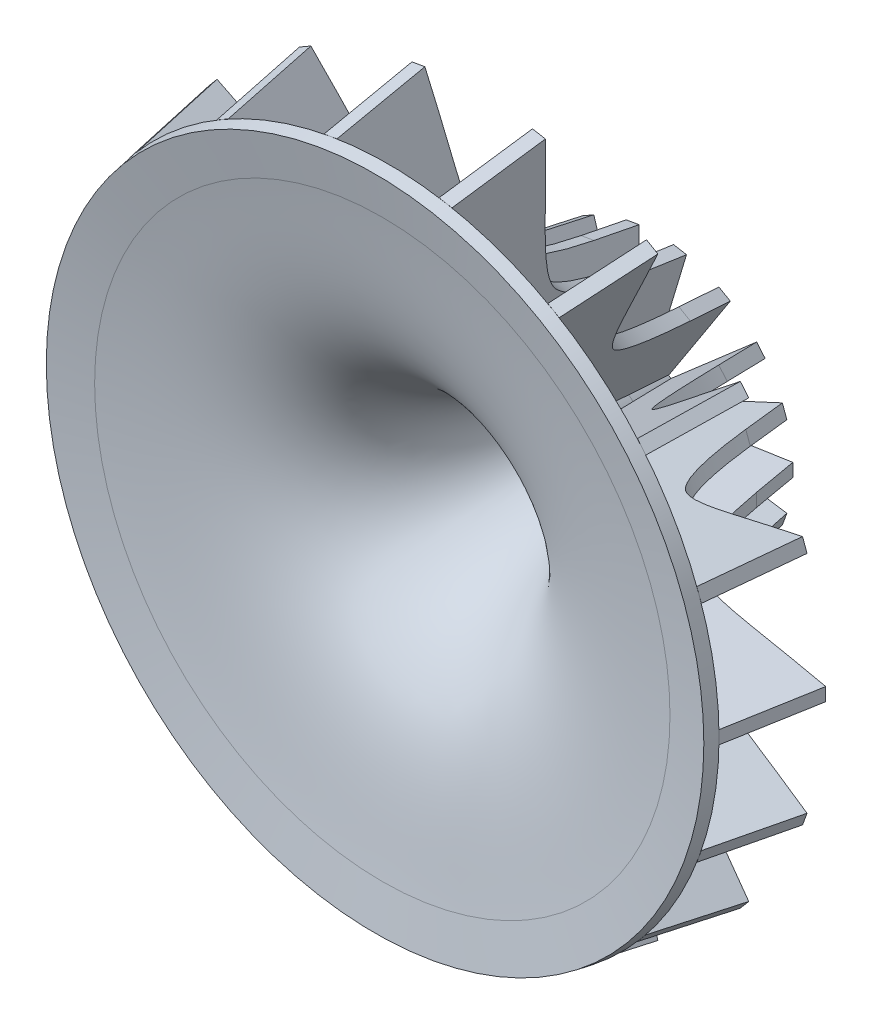
SolidWorks part; units mm, degrees
ref_plane "Front Plane" through (0, 0, 0) normal (0, 0, 1) x (1, 0, 0)
ref_plane "Top Plane" through (0, 0, 0) normal (0, 1, 0) x (1, 0, 0)
ref_plane "Right Plane" through (0, 0, 0) normal (1, 0, 0) x (0, 0, -1)
sketch "Sketch_of_Hub" plane through (0, 0, 0) normal (0, 1, 0) x (1, 0, 0)
  line L0 (-25, 0) -> (-21.875, 0.551)
  line L1 (-25, 0) -> (-2.5, 0) construction
  line L2 (-3.0878, 16.6667) -> (-2.5, 20)
  line L3 (-2.5, 0) -> (-2.5, 20) construction
  line L4 (-25.1736, 0.9848) -> (-22.0486, 1.5358)
  line L5 (-4.0726, 16.8403) -> (-3.4848, 20.1736)
  line L6 (-3.4848, 20.1736) -> (-2.5, 20)
  line L7 (-25.1736, 0.9848) -> (-25, 0)
  line L8 (0, -11.4107) -> (0, -1.4179) construction
  spline S0 degree 1 poles (-22.0486, 1.5358) (-4.0726, 16.8403) knots 0 0 1 1 construction
  spline S1 degree 3 poles (-21.875, 0.551) (-12.6553, 2.1767) (-5.6751, 1.9929) (-3.0878, 16.6667) knots 0 0 0 0 1 1 1 1
  spline S2 degree 3 poles (-22.0486, 1.5358) (-21.4781, 1.6364) (-20.318, 1.8298) (-18.1331, 2.1821) (-15.5731, 2.6349) (-12.8414, 3.3758) (-10.4654, 4.4784) (-8.4179, 6.109) (-6.9387, 8.1051) (-5.898, 10.2171) (-5.1966, 12.0843) (-4.6823, 13.9057) (-4.3193, 15.5169) (-4.1493, 16.4049) (-4.0726, 16.8403) knots 0 0 0 0 0.0625 0.125 0.25 0.375 0.5 0.625 0.75 0.8125 0.875 0.9375 0.96875 1 1 1 1
  dimension "D1" = 2.5
  dimension "D2" = 20
  dimension "D3" = 25
  dimension "D4" = 10
  dimension "D5" = 10
  dimension "D7" = 3.3333
  dimension "D8" = 3.125
  dimension "D6" = 1
revolve "Hub" add sketch "Sketch_of_Hub" angle 360 about L8
sketch "Sketch9" plane through (0, 0, 0) normal (0, 1, 0) x (1, 0, 0)
  line L0 (-10.3785, 21.3892) -> (-10.9662, 18.0559)
  line L1 (-23.2642, 8.4295) -> (-26.3892, 7.8785)
  line L2 (-3.4848, 20.1736) -> (-10.3785, 21.3892)
  line L3 (-26.3892, 7.8785) -> (-25.1736, 0.9848)
  line L6 (-3.4848, 20.1736) -> (-4.0726, 16.8403)
  line L7 (-2.5, 20) -> (-3.4848, 20.1736)
  line L8 (-3.0878, 16.6667) -> (-2.5, 20)
  line L9 (-25, 0) -> (-21.875, 0.551)
  line L10 (-25.1736, 0.9848) -> (-25, 0)
  line L11 (-22.0486, 1.5358) -> (-25.1736, 0.9848)
  line L18 (-3.4848, 20.1736) -> (-4.0726, 16.8403)
  line L23 (-22.0486, 1.5358) -> (-25.1736, 0.9848)
  spline S0 degree 1 poles (-10.9662, 18.0559) (-23.2642, 8.4295) knots 0 0 1 1 construction
  spline S1 degree 3 poles (-10.9662, 18.0559) (-11.0308, 17.6896) (-11.1758, 16.9329) (-11.4686, 15.6357) (-11.8669, 14.2333) (-12.3467, 12.9687) (-12.9591, 11.7427) (-13.5694, 10.9776) (-14.1233, 10.5317) (-15.1348, 10.0236) (-16.689, 9.584) (-18.3596, 9.2514) (-19.8108, 9.002) (-21.4281, 8.7414) (-22.6662, 8.5349) (-23.2642, 8.4295) knots 0 0 0 0 0.03125 0.0625 0.125 0.1875 0.25 0.375 0.5 0.625 0.75 0.8125 0.875 0.9375 1 1 1 1
  spline S2 degree 3 poles (-106.1325, -995.8881) (-142.0874, 977.9655) (179.6787, -978.0787) (-157.3539, 1004.6818) knots -3.780329 -3.780329 -3.780329 -3.780329 4.006276 4.006276 4.006276 4.006276 only from (-21.875, 0.551) to (-3.0878, 16.6667)
  spline S3 degree 3 poles (-776.0265, -3907.7228) (-2.9928, 116.0692) (0.3333, 36.1691) (-4.6823, 13.9057) (-5.1966, 12.0843) (-5.898, 10.2171) (-6.9387, 8.1051) (-8.4179, 6.109) (-10.4654, 4.4784) (-12.8414, 3.3758) (-15.5731, 2.6349) (-18.1331, 2.1821) (-49.4462, -2.8661) (-131.4903, -20.9757) (3977.7068, 16.8999) knots -1.60226 -1.60226 -1.60226 -1.60226 0.03125 0.0625 0.125 0.1875 0.25 0.375 0.5 0.625 0.75 0.875 0.9375 4.333013 4.333013 4.333013 4.333013 only from (-4.0726, 16.8403) to (-22.0486, 1.5358)
  spline S5 degree 3 poles (-4.0726, 16.8403) (-4.1493, 16.4049) (-4.3193, 15.5169) (-4.6823, 13.9057) (-5.1966, 12.0843) (-5.898, 10.2171) (-6.9387, 8.1051) (-8.4179, 6.109) (-10.4654, 4.4784) (-12.8414, 3.3758) (-15.5731, 2.6349) (-18.1331, 2.1821) (-20.318, 1.8298) (-21.4781, 1.6364) (-22.0486, 1.5358) knots 0 0 0 0 0.03125 0.0625 0.125 0.1875 0.25 0.375 0.5 0.625 0.75 0.875 0.9375 1 1 1 1
  dimension "D1" = 0
  dimension "D2" = 7
extrude "Blade" add sketch "Sketch9" along normal mid plane 1 separate body
pattern_circular "Blade_Pattern" count 18 over 360 about axis through (0, 0, -20.1736) along (0, 0, 1) of bodies 102
equation "\"Hub_Vertical_Angle\"= 10"
equation "\"Hub_Horizontal_Angle\"=10"
equation "\"Hub_Hole_Radius\"= 2.5"
equation "\"Hub_Radius\"= 25"
equation "\"Hub_Height\"= 20"
equation "\"D2@Sketch_of_Hub\" = \"Hub_Height\""
equation "\"D3@Sketch_of_Hub\" = \"Hub_Radius\""
equation "\"D1@Sketch_of_Hub\" = \"Hub_Hole_Radius\""
equation "\"D4@Sketch_of_Hub\" = \"Hub_Horizontal_Angle\""
equation "\"D5@Sketch_of_Hub\" = \"Hub_Vertical_Angle\""
equation "\"Mouth_Vertical_Height\"= \"Hub_Height\" * 1 / 6"
equation "\"D7@Sketch_of_Hub\"=\"Mouth_Vertical_Height\""
equation "\"Exit_Horizontal_Length\"= \"Hub_Radius\" * 1 / 8"
equation "\"D8@Sketch_of_Hub\"=\"Exit_Horizontal_Length\""
